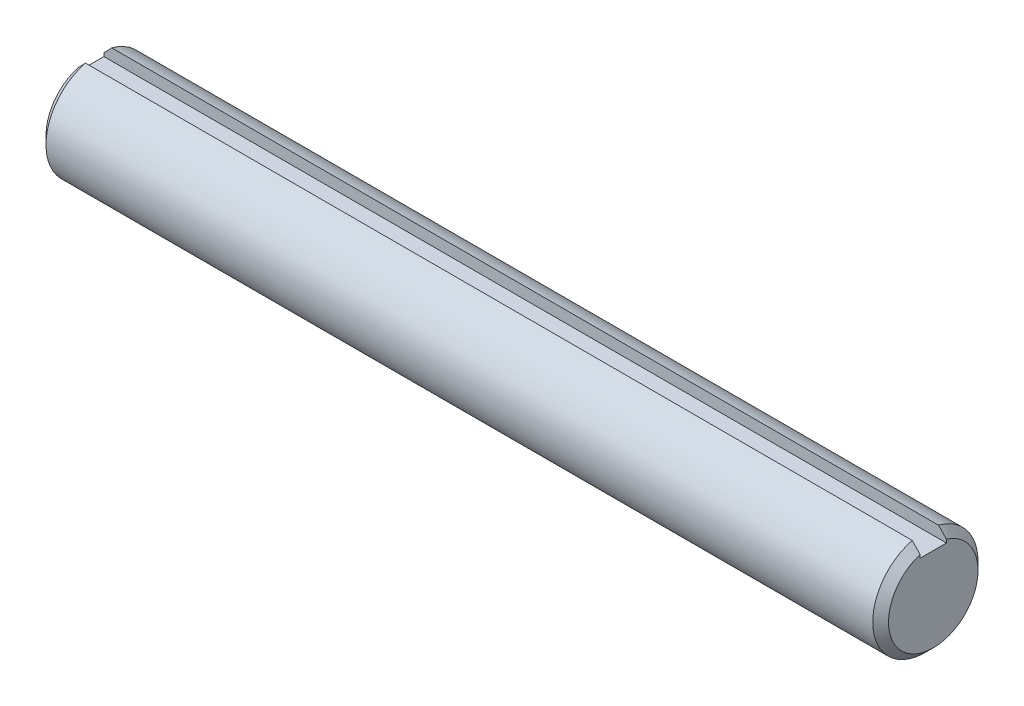
SolidWorks part; units mm, degrees
material "AISI 1045 Steel, cold drawn"
ref_plane "Front" through (0, 0, 0) normal (0, 0, 1) x (1, 0, 0)
ref_plane "Top" through (0, 0, 0) normal (0, 1, 0) x (1, 0, 0)
ref_plane "Right" through (0, 0, 0) normal (1, 0, 0) x (0, 0, -1)
sketch "Sketch1" plane through (0, 0, 0) normal (1, 0, 0) x (0, 0, -1)
  circle A0 centre (0, 0) radius 19.05
  dimension "dia" = 38.1
extrude "Extrude1" add sketch "Sketch1" along normal mid plane 304.8
sketch "Sketch2" plane through (0, 0, 0) normal (0, 0, 1) x (1, 0, 0)
  point P0 (152.4, 19.05)
  point P1 (-152.4, 19.05)
  point P2 (-152.4, -19.05)
chamfer "Chamfer1" distance 2.8575 angle 45 2 edges at (-152.4, 0, -19.05) (152.4, 0, -19.05)
sketch "Sketch3" plane through (0, 0, 0) normal (-1, 0, 0) x (0, 0, 1)
  line L1 (-4.7625, 19.05) -> (4.7625, 19.05)
  line L2 (-4.7625, 19.05) -> (-4.7625, 14.2875)
  line L3 (-4.7625, 14.2875) -> (4.7625, 14.2875)
  line L4 (4.7625, 19.05) -> (4.7625, 14.2875)
  dimension "key wd" = 9.525
  dimension "key dp" = 4.7625
extrude "Extrude2" cut sketch "Sketch3" against normal through all and the other way through all
equation "\"D1@Chamfer1\" = \"dia@Sketch1\" * .075"
